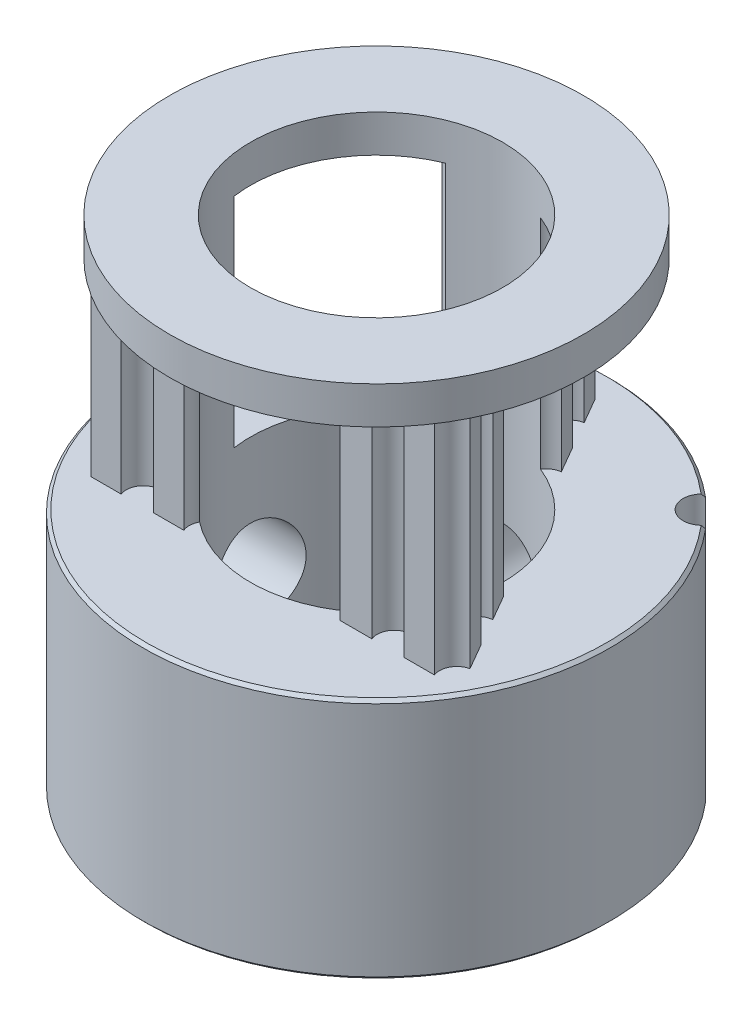
SolidWorks part; units mm, degrees
material "6061 slitina"
ref_plane "Přední rovina" through (0, 0, 0) normal (0, 0, 1) x (1, 0, 0)
ref_plane "Horní rovina" through (0, 0, 0) normal (0, 1, 0) x (1, 0, 0)
ref_plane "Pravá rovina" through (0, 0, 0) normal (1, 0, 0) x (0, 0, -1)
sketch "Skica1" plane through (0, 0, 0) normal (0, 1, 0) x (1, 0, 0)
  circle A0 centre (0, 0) radius 2.5
  arc B0 (-5.7301, 1.0983) -> (-5.3872, 2.2403) centre (-5.6803, 1.7058) ccw
  arc B1 (-5.7301, 1.0983) -> (-5.922, 1.0859) centre (-5.7841, 0.4401) ccw
  arc B2 (-5.922, 1.0859) -> (-6.0197, 1.0387) centre (-5.8743, 0.8624) ccw
  arc B3 (-6.0197, 1.0387) -> (-6.0791, 0.6004) centre (0, 0) ccw
  arc B4 (-6.0791, 0.6004) -> (-5.9974, 0.5289) centre (-5.892, 0.7317) ccw
  arc B5 (-5.9974, 0.5289) -> (-5.8158, 0.466) centre (-5.6927, 1.1148) ccw
  arc B6 (-5.7891, -0.7262) -> (-5.8158, 0.466) centre (-5.9294, -0.133) ccw
  arc B7 (-5.7891, -0.7262) -> (-5.9677, -0.7972) centre (-5.637, -1.3689) ccw
  arc B8 (-5.9677, -0.7972) -> (-6.0461, -0.8723) centre (-5.8532, -0.9951) ccw
  arc B9 (-6.0461, -0.8723) -> (-5.9671, -1.3075) centre (0, 0) ccw
  arc B10 (-5.9671, -1.3075) -> (-5.8673, -1.3503) centre (-5.8297, -1.1248) ccw
  arc B11 (-5.8673, -1.3503) -> (-5.6751, -1.354) centre (-5.7586, -0.6989) ccw
  arc B12 (-5.2813, -2.4796) -> (-5.6751, -1.354) centre (-5.5981, -1.9587) ccw
  arc B13 (-5.2813, -2.4796) -> (-5.4293, -2.6023) centre (-4.9381, -3.0438) ccw
  arc B14 (-5.4293, -2.6023) -> (-5.4806, -2.698) centre (-5.2593, -2.7551) ccw
  arc B15 (-5.4806, -2.698) -> (-5.271, -3.0875) centre (0, 0) ccw
  arc B16 (-5.271, -3.0875) -> (-5.1629, -3.0973) centre (-5.1968, -2.8713) ccw
  arc B17 (-5.1629, -3.0973) -> (-4.979, -3.0415) centre (-5.2608, -2.4442) ccw
  arc B18 (-4.2566, -3.9902) -> (-4.979, -3.0415) centre (-4.7188, -3.5928) ccw
  arc B19 (-4.2566, -3.9902) -> (-4.3594, -4.1527) centre (-3.7559, -4.4208) ccw
  arc B20 (-4.3594, -4.1527) -> (-4.3786, -4.2595) centre (-4.1505, -4.2455) ccw
  arc B21 (-4.3786, -4.2595) -> (-4.059, -4.5652) centre (0, 0) ccw
  arc B22 (-4.059, -4.5652) -> (-3.9531, -4.5412) centre (-4.0552, -4.3366) ccw
  arc B23 (-3.9531, -4.5412) -> (-3.7954, -4.4312) centre (-4.248, -3.9503) ccw
  arc B24 (-2.8152, -5.1103) -> (-3.7954, -4.4312) centre (-3.3776, -4.8751) ccw
  arc B25 (-2.8152, -5.1103) -> (-2.8628, -5.2965) centre (-2.2059, -5.3651) ccw
  arc B26 (-2.8628, -5.2965) -> (-2.8481, -5.4041) centre (-2.6354, -5.3203) ccw
  arc B27 (-2.8481, -5.4041) -> (-2.4496, -5.596) centre (0, 0) ccw
  arc B28 (-2.4496, -5.596) -> (-2.3563, -5.5405) centre (-2.5166, -5.3775) ccw
  arc B29 (-2.3563, -5.5405) -> (-2.2403, -5.3872) centre (-2.8194, -5.0696) ccw
  arc B30 (-1.0983, -5.7301) -> (-2.2403, -5.3872) centre (-1.7058, -5.6803) ccw
  arc B31 (-1.0983, -5.7301) -> (-1.0859, -5.922) centre (-0.4401, -5.7841) ccw
  arc B32 (-1.0859, -5.922) -> (-1.0387, -6.0197) centre (-0.8624, -5.8743) ccw
  arc B33 (-1.0387, -6.0197) -> (-0.6004, -6.0791) centre (0, 0) ccw
  arc B34 (-0.6004, -6.0791) -> (-0.5289, -5.9974) centre (-0.7317, -5.892) ccw
  arc B35 (-0.5289, -5.9974) -> (-0.466, -5.8158) centre (-1.1148, -5.6927) ccw
  arc B36 (0.7262, -5.7891) -> (-0.466, -5.8158) centre (0.133, -5.9294) ccw
  arc B37 (0.7262, -5.7891) -> (0.7972, -5.9677) centre (1.3689, -5.637) ccw
  arc B38 (0.7972, -5.9677) -> (0.8723, -6.0461) centre (0.9951, -5.8532) ccw
  arc B39 (0.8723, -6.0461) -> (1.3075, -5.9671) centre (0, 0) ccw
  arc B40 (1.3075, -5.9671) -> (1.3503, -5.8673) centre (1.1248, -5.8297) ccw
  arc B41 (1.3503, -5.8673) -> (1.354, -5.6751) centre (0.6989, -5.7586) ccw
  arc B42 (2.4796, -5.2813) -> (1.354, -5.6751) centre (1.9587, -5.5981) ccw
  arc B43 (2.4796, -5.2813) -> (2.6023, -5.4293) centre (3.0438, -4.9381) ccw
  arc B44 (2.6023, -5.4293) -> (2.698, -5.4806) centre (2.7551, -5.2593) ccw
  arc B45 (2.698, -5.4806) -> (3.0875, -5.271) centre (0, 0) ccw
  arc B46 (3.0875, -5.271) -> (3.0973, -5.1629) centre (2.8713, -5.1968) ccw
  arc B47 (3.0973, -5.1629) -> (3.0415, -4.979) centre (2.4442, -5.2608) ccw
  arc B48 (3.9902, -4.2566) -> (3.0415, -4.979) centre (3.5928, -4.7188) ccw
  arc B49 (3.9902, -4.2566) -> (4.1527, -4.3594) centre (4.4208, -3.7559) ccw
  arc B50 (4.1527, -4.3594) -> (4.2595, -4.3786) centre (4.2455, -4.1505) ccw
  arc B51 (4.2595, -4.3786) -> (4.5652, -4.059) centre (0, 0) ccw
  arc B52 (4.5652, -4.059) -> (4.5412, -3.9531) centre (4.3366, -4.0552) ccw
  arc B53 (4.5412, -3.9531) -> (4.4312, -3.7954) centre (3.9503, -4.248) ccw
  arc B54 (5.1103, -2.8152) -> (4.4312, -3.7954) centre (4.8751, -3.3776) ccw
  arc B55 (5.1103, -2.8152) -> (5.2965, -2.8628) centre (5.3651, -2.2059) ccw
  arc B56 (5.2965, -2.8628) -> (5.4041, -2.8481) centre (5.3203, -2.6354) ccw
  arc B57 (5.4041, -2.8481) -> (5.596, -2.4496) centre (0, 0) ccw
  arc B58 (5.596, -2.4496) -> (5.5405, -2.3563) centre (5.3775, -2.5166) ccw
  arc B59 (5.5405, -2.3563) -> (5.3872, -2.2403) centre (5.0696, -2.8194) ccw
  arc B60 (5.7301, -1.0983) -> (5.3872, -2.2403) centre (5.6803, -1.7058) ccw
  arc B61 (5.7301, -1.0983) -> (5.922, -1.0859) centre (5.7841, -0.4401) ccw
  arc B62 (5.922, -1.0859) -> (6.0197, -1.0387) centre (5.8743, -0.8624) ccw
  arc B63 (6.0197, -1.0387) -> (6.0791, -0.6004) centre (0, 0) ccw
  arc B64 (6.0791, -0.6004) -> (5.9974, -0.5289) centre (5.892, -0.7317) ccw
  arc B65 (5.9974, -0.5289) -> (5.8158, -0.466) centre (5.6927, -1.1148) ccw
  arc B66 (5.7891, 0.7262) -> (5.8158, -0.466) centre (5.9294, 0.133) ccw
  arc B67 (5.7891, 0.7262) -> (5.9677, 0.7972) centre (5.637, 1.3689) ccw
  arc B68 (5.9677, 0.7972) -> (6.0461, 0.8723) centre (5.8532, 0.9951) ccw
  arc B69 (6.0461, 0.8723) -> (5.9671, 1.3075) centre (0, 0) ccw
  arc B70 (5.9671, 1.3075) -> (5.8673, 1.3503) centre (5.8297, 1.1248) ccw
  arc B71 (5.8673, 1.3503) -> (5.6751, 1.354) centre (5.7586, 0.6989) ccw
  arc B72 (5.2813, 2.4796) -> (5.6751, 1.354) centre (5.5981, 1.9587) ccw
  arc B73 (5.2813, 2.4796) -> (5.4293, 2.6023) centre (4.9381, 3.0438) ccw
  arc B74 (5.4293, 2.6023) -> (5.4806, 2.698) centre (5.2593, 2.7551) ccw
  arc B75 (5.4806, 2.698) -> (5.271, 3.0875) centre (0, 0) ccw
  arc B76 (5.271, 3.0875) -> (5.1629, 3.0973) centre (5.1968, 2.8713) ccw
  arc B77 (5.1629, 3.0973) -> (4.979, 3.0415) centre (5.2608, 2.4442) ccw
  arc B78 (4.2566, 3.9902) -> (4.979, 3.0415) centre (4.7188, 3.5928) ccw
  arc B79 (4.2566, 3.9902) -> (4.3594, 4.1527) centre (3.7559, 4.4208) ccw
  arc B80 (4.3594, 4.1527) -> (4.3786, 4.2595) centre (4.1505, 4.2455) ccw
  arc B81 (4.3786, 4.2595) -> (4.059, 4.5652) centre (0, 0) ccw
  arc B82 (4.059, 4.5652) -> (3.9531, 4.5412) centre (4.0552, 4.3366) ccw
  arc B83 (3.9531, 4.5412) -> (3.7954, 4.4312) centre (4.248, 3.9503) ccw
  arc B84 (2.8152, 5.1103) -> (3.7954, 4.4312) centre (3.3776, 4.8751) ccw
  arc B85 (2.8152, 5.1103) -> (2.8628, 5.2965) centre (2.2059, 5.3651) ccw
  arc B86 (2.8628, 5.2965) -> (2.8481, 5.4041) centre (2.6354, 5.3203) ccw
  arc B87 (2.8481, 5.4041) -> (2.4496, 5.596) centre (0, 0) ccw
  arc B88 (2.4496, 5.596) -> (2.3563, 5.5405) centre (2.5166, 5.3775) ccw
  arc B89 (2.3563, 5.5405) -> (2.2403, 5.3872) centre (2.8194, 5.0696) ccw
  arc B90 (1.0983, 5.7301) -> (2.2403, 5.3872) centre (1.7058, 5.6803) ccw
  arc B91 (1.0983, 5.7301) -> (1.0859, 5.922) centre (0.4401, 5.7841) ccw
  arc B92 (1.0859, 5.922) -> (1.0387, 6.0197) centre (0.8624, 5.8743) ccw
  arc B93 (1.0387, 6.0197) -> (0.6004, 6.0791) centre (0, 0) ccw
  arc B94 (0.6004, 6.0791) -> (0.5289, 5.9974) centre (0.7317, 5.892) ccw
  arc B95 (0.5289, 5.9974) -> (0.466, 5.8158) centre (1.1148, 5.6927) ccw
  arc B96 (-0.7262, 5.7891) -> (0.466, 5.8158) centre (-0.133, 5.9294) ccw
  arc B97 (-0.7262, 5.7891) -> (-0.7972, 5.9677) centre (-1.3689, 5.637) ccw
  arc B98 (-0.7972, 5.9677) -> (-0.8723, 6.0461) centre (-0.9951, 5.8532) ccw
  arc B99 (-0.8723, 6.0461) -> (-1.3075, 5.9671) centre (0, 0) ccw
  arc B100 (-1.3075, 5.9671) -> (-1.3503, 5.8673) centre (-1.1248, 5.8297) ccw
  arc B101 (-1.3503, 5.8673) -> (-1.354, 5.6751) centre (-0.6989, 5.7586) ccw
  arc B102 (-2.4796, 5.2813) -> (-1.354, 5.6751) centre (-1.9587, 5.5981) ccw
  arc B103 (-2.4796, 5.2813) -> (-2.6023, 5.4293) centre (-3.0438, 4.9381) ccw
  arc B104 (-2.6023, 5.4293) -> (-2.698, 5.4806) centre (-2.7551, 5.2593) ccw
  arc B105 (-2.698, 5.4806) -> (-3.0875, 5.271) centre (0, 0) ccw
  arc B106 (-3.0875, 5.271) -> (-3.0973, 5.1629) centre (-2.8713, 5.1968) ccw
  arc B107 (-3.0973, 5.1629) -> (-3.0415, 4.979) centre (-2.4442, 5.2608) ccw
  arc B108 (-3.9902, 4.2566) -> (-3.0415, 4.979) centre (-3.5928, 4.7188) ccw
  arc B109 (-3.9902, 4.2566) -> (-4.1527, 4.3594) centre (-4.4208, 3.7559) ccw
  arc B110 (-4.1527, 4.3594) -> (-4.2595, 4.3786) centre (-4.2455, 4.1505) ccw
  arc B111 (-4.2595, 4.3786) -> (-4.5652, 4.059) centre (0, 0) ccw
  arc B112 (-4.5652, 4.059) -> (-4.5412, 3.9531) centre (-4.3366, 4.0552) ccw
  arc B113 (-4.5412, 3.9531) -> (-4.4312, 3.7954) centre (-3.9503, 4.248) ccw
  arc B114 (-5.1103, 2.8152) -> (-4.4312, 3.7954) centre (-4.8751, 3.3776) ccw
  arc B115 (-5.1103, 2.8152) -> (-5.2965, 2.8628) centre (-5.3651, 2.2059) ccw
  arc B116 (-5.2965, 2.8628) -> (-5.4041, 2.8481) centre (-5.3203, 2.6354) ccw
  arc B117 (-5.4041, 2.8481) -> (-5.596, 2.4496) centre (0, 0) ccw
  arc B118 (-5.596, 2.4496) -> (-5.5405, 2.3563) centre (-5.3775, 2.5166) ccw
  arc B119 (-5.5405, 2.3563) -> (-5.3872, 2.2403) centre (-5.0696, 2.8194) ccw
  dimension "D1" = 5
sketch_block_instance "Blok1-1"
sketch_block "Blok1"
extrude "Přidat vysunutím1" add sketch "Skica1" along normal blind 7 from offset 7.8
sketch "Skica2" plane through (0, 7.8, 0) normal (0, -1, 0) x (1, 0, 0)
  circle A0 centre (0, 0) radius 3.5
  circle A1 centre (0, 0) radius 2.5 construction
  circle A2 centre (0, 0) radius 2.5
  dimension "D1" = 7
extrude "Přidat vysunutím2" add sketch "Skica2" along normal blind 7.8
sketch "Skica3" plane through (0, 14.8, 0) normal (0, 1, 0) x (1, 0, 0)
  circle A0 centre (0, 0) radius 3.5
  circle A1 centre (0, 0) radius 2.5 construction
  circle A2 centre (0, 0) radius 2.5
  dimension "D1" = 7
extrude "Přidat vysunutím3" add sketch "Skica3" along normal blind 1.2
sketch "Skica5" plane through (0, 16, 0) normal (0, 1, 0) x (1, 0, 0)
  circle A0 centre (0, 0) radius 7.5
  circle A3 centre (0, 0) radius 3.5 construction
  circle A4 centre (0, 0) radius 3.5
  dimension "D1" = 15
extrude "Přidat vysunutím4" add sketch "Skica5" against normal up to surface (1.2 mm away) separate body up to face at (0, 14.8, 0)
sketch "Skica6" plane through (0, 0, 0) normal (0, -1, 0) x (1, 0, 0)
  circle A0 centre (0, 0) radius 7.5
  circle A1 centre (0, 0) radius 3.5 construction
  circle A2 centre (0, 0) radius 3.5
  circle A3 centre (0, 0) radius 7.5 construction
extrude "Přidat vysunutím5" add sketch "Skica6" against normal up to surface (7.8 mm away) separate body up to face at (0, 7.8, 0)
chamfer "Zkosení1" distance 0.1 angle 45 2 edges at (0, 14.8, 7.5) (0, 16, 7.5)
chamfer "Zkosení2" distance 0.1 angle 45 2 edges at (0, 0, -2.5) (0, 16, 2.5)
chamfer "Zkosení3" distance 0.1 angle 45 2 edges at (0, 0, -7.5) (0, 7.8, 7.5)
sketch "Sketch7" plane through (0, 0, 0) normal (0, -1, 0) x (1, 0, 0)
  circle A1 centre (0, 0) radius 4.05
  dimension "D1" = 8.1
sketch "Sketch8" plane through (0, 16, 0) normal (0, 1, 0) x (1, 0, 0)
  circle A0 centre (0, 0) radius 6.65
extrude "Cut-Extrude2" cut sketch "Sketch8" against normal blind 5 flip side to cut contours A0
ref_plane "Plane1" through (0, 0, -7.5) normal (0, 0, -1) x (-1, 0, 0)
ref_plane "Plane2" through (-7.5, 0, 0) normal (-1, 0, 0) x (0, 0, 1)
sketch "Sketch19" plane through (0, 0, -7.5) normal (0, 0, -1) x (-1, 0, 0)
  line L0 (0, 0.1) -> (0, 7.7)
  line L1 (7.5, 0.1) -> (-7.5, 0.1) construction
  line L2 (7.5, 7.7) -> (-7.5, 7.7) construction
  circle A0 centre (0, 3.9) radius 1.5
extrude "Cut-Extrude6" cut sketch "Sketch19" against normal blind 5 contours A0
sketch "Sketch20" plane through (-7.5, 0, 0) normal (-1, 0, 0) x (0, 0, 1)
  line L0 (0, 0.1) -> (0, 7.7)
  line L1 (-7.5, 0.1) -> (7.5, 0.1) construction
  line L2 (7.5, 7.7) -> (-7.5, 7.7) construction
  circle A0 centre (0, 3.9) radius 1.5
extrude "Cut-Extrude7" cut sketch "Sketch20" against normal blind 5 contours A0
extrude "Cut-Extrude9" cut sketch "Sketch7" against normal blind 20 contours A1
sketch "Sketch23" plane through (0, 0, 0) normal (0, 1, 0) x (1, 0, 0)
  line L1 (0, 7.34) -> (-6.3566, -3.67)
  line L2 (-6.3566, -3.67) -> (6.3566, -3.67)
  line L3 (6.3566, -3.67) -> (0, 7.34)
  circle A0 centre (0, 0) radius 3.67 construction
sketch "Sketch25" plane through (0, 7.8, 0) normal (0, 1, 0) x (1, 0, 0)
  line L0 (-0.7179, 6.0965) -> (-0.9071, 5.7689)
  line L5 (-5.5084, -3.67) -> (-4.5368, -3.67)
  line L6 (5.926, -2.9242) -> (5.4338, -2.0716)
  line L9 (-5.4363, -2.0759) -> (-5.8989, -2.8773)
  line L23 (-3.4987, -3.67) -> (-2.5208, -3.67)
  line L24 (-4.4422, -0.3541) -> (-4.912, -1.1678)
  line L26 (-1.4992, -3.67) -> (-0.513, -3.67)
  line L27 (2.4958, -3.67) -> (3.5189, -3.67)
  line L28 (4.926, -1.192) -> (4.4459, -0.3606)
  line L29 (4.549, -3.67) -> (5.5306, -3.67)
  line L30 (0.5086, -3.67) -> (1.4742, -3.67)
  line L31 (3.9112, 0.5657) -> (3.4185, 1.419)
  line L32 (1.9163, 4.0209) -> (1.4364, 4.8521)
  line L33 (-1.4233, 4.8748) -> (-1.9185, 4.0171)
  line L34 (2.9152, 2.2908) -> (2.4274, 3.1357)
  line L35 (0.9141, 5.7568) -> (0.4321, 6.5916)
  line L37 (-2.4409, 3.1122) -> (-2.9162, 2.2891)
  line L39 (-0.7179, 6.0965) -> (-0.4321, 6.5916)
  line L40 (-3.4352, 1.3901) -> (-3.9277, 0.5371)
  line L42 (-0.4321, 6.5916) -> (-0.9071, 5.7689) [skipped]
  arc A24 (-0.4321, 6.5916) -> (0.4321, 6.5916) centre (0, 6.94) ccw
  arc A25 (-1.4233, 4.8748) -> (-0.9071, 5.7689) centre (-0.9887, 5.22) ccw
  arc A26 (-2.4409, 3.1122) -> (-1.9185, 4.0171) centre (-2.0176, 3.471) ccw
  arc A27 (0.9141, 5.7568) -> (1.4364, 4.8521) centre (1.0128, 5.2106) ccw
  arc A28 (1.9163, 4.0209) -> (2.4274, 3.1357) centre (1.9844, 3.4701) ccw
  arc A29 (-3.4352, 1.3901) -> (-2.9162, 2.2891) centre (-3.0054, 1.7413) ccw
  arc A30 (-4.4422, -0.3541) -> (-3.9277, 0.5371) centre (-4.0048, -0.0125) ccw
  arc A31 (-5.4363, -2.0759) -> (-4.912, -1.1678) centre (-5.0165, -1.7129) ccw
  arc A32 (-5.5084, -3.67) -> (-5.8989, -2.8773) centre (-6.0049, -3.4221) ccw
  arc A33 (-3.4987, -3.67) -> (-4.5368, -3.67) centre (-4.0177, -3.4735) ccw
  arc A34 (-1.4992, -3.67) -> (-2.5208, -3.67) centre (-2.01, -3.4529) ccw
  arc A35 (0.5086, -3.67) -> (-0.513, -3.67) centre (-0.0022, -3.4529) ccw
  arc A36 (2.4958, -3.67) -> (1.4742, -3.67) centre (1.985, -3.4529) ccw
  arc A37 (4.549, -3.67) -> (3.5189, -3.67) centre (4.0339, -3.4632) ccw
  arc A38 (2.9152, 2.2908) -> (3.4185, 1.419) centre (2.9643, 1.738) ccw
  arc A39 (3.9112, 0.5657) -> (4.4459, -0.3606) centre (4.05, 0.0283) ccw
  arc A40 (4.926, -1.192) -> (5.4338, -2.0716) centre (4.9859, -1.7438) ccw
  arc A41 (5.926, -2.9242) -> (5.5306, -3.67) centre (6.0467, -3.4659) ccw
  point P0 (-1.0017, 5.205)
  point P6 (-2.0034, 3.47)
  point P7 (-3.0051, 1.735)
  point P9 (-4.0068, 0)
  point P10 (-5.0085, -1.735)
  point P11 (5.0085, -1.735)
  point P12 (4.0068, 0)
  point P13 (3.0051, 1.735)
  point P14 (2.0034, 3.47)
  point P15 (1.0017, 5.205)
  point P16 (-4.0068, -3.47)
  point P20 (-2.0034, -3.47)
  point P21 (0, -3.47)
  point P23 (2.0034, -3.47)
  point P24 (4.0068, -3.47)
sketch "Sketch27" plane through (0, 7.8, 0) normal (0, 1, 0) x (1, 0, 0)
  circle A0 centre (0, 0) radius 7.4
extrude "Cut-Extrude12" cut sketch "Sketch27" along normal blind 7 contours A0
extrude "Boss-Extrude2" add sketch "Sketch25" along normal blind 7.1 contours L33 A26 L37 A29 L40 A30 L24 A31 L9 A32 L5 A33 L23 A34 L26 A35 L30 A36 L27 A37 L29 A41 L6 A40 L28 A39 L31 A38 L34 A28 L32 A27 L35 A24 L39 L0 A25
sketch "Sketch28" plane through (0, 16, 0) normal (0, 1, 0) x (1, 0, 0)
  circle A0 centre (0, 0) radius 4.05
extrude "Cut-Extrude13" cut sketch "Sketch28" against normal blind 30
sketch "Sketch30" plane through (0, 0, 0) normal (0, -1, 0) x (1, 0, 0)
  line L0 (0, 0) -> (6.782, 0)
  line L1 (6.782, 0) -> (0, -6.782)
  line L2 (-0.1186, 0) -> (3.391, -3.391)
  line L3 (3.391, -3.391) -> (4.7956, -4.7956)
  line L4 (4.7956, -4.7956) -> (5.2326, -5.2326)
  circle A0 centre (0, 0) radius 6.782
  circle A1 centre (0, 0) radius 7.4 construction
  circle A2 centre (5.2326, -5.2326) radius 0.618
extrude "Cut-Extrude15" cut sketch "Sketch30" against normal blind 30 contours A2
